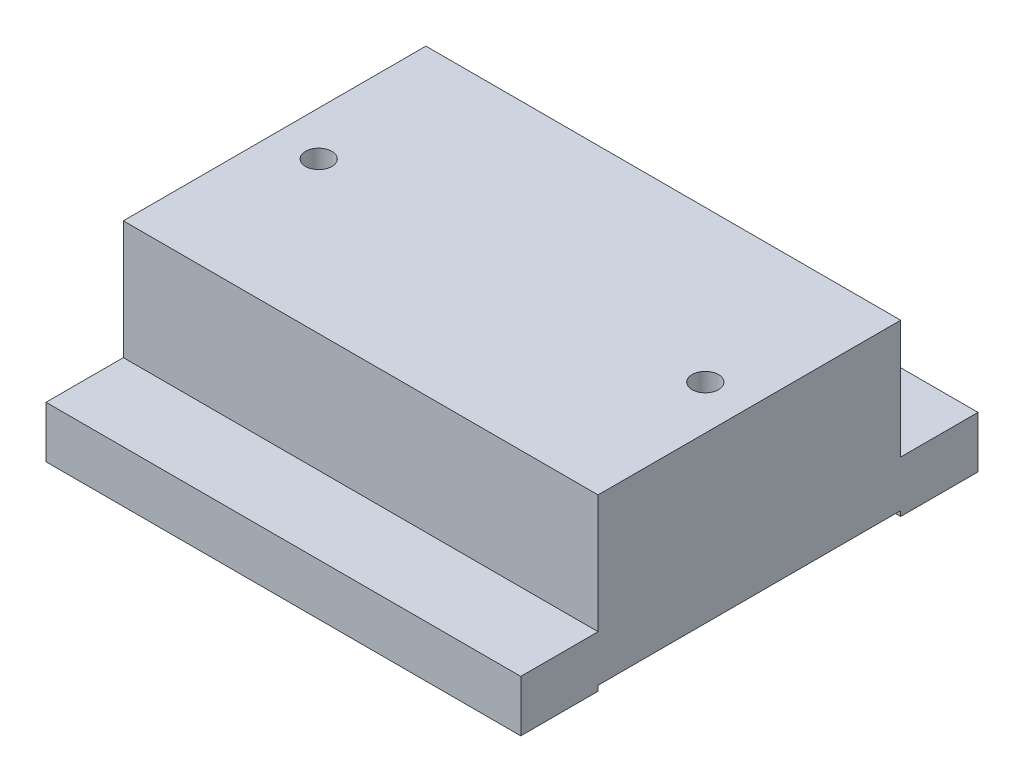
SolidWorks part; units mm, degrees
material "6061 Alloy"
ref_plane "Front" through (0, 0, 0) normal (0, 0, 1) x (1, 0, 0)
ref_plane "Top" through (0, 0, 0) normal (0, 1, 0) x (1, 0, 0)
ref_plane "Right" through (0, 0, 0) normal (1, 0, 0) x (0, 0, -1)
sketch "Sketch1" plane through (0, 0, 0) normal (0, 1, 0) x (1, 0, 0)
  line L1 (-46.05, 44.35) -> (46.05, 44.35)
  line L2 (-46.05, 44.35) -> (-46.05, -44.35)
  line L3 (-46.05, -44.35) -> (46.05, -44.35)
  line L4 (46.05, 44.35) -> (46.05, -44.35)
  line L5 (-46.05, 44.35) -> (46.05, -44.35) construction
  line L6 (-46.05, -44.35) -> (46.05, 44.35) construction
  point P0 (0, 0)
  dimension "D1" = 92.1
  dimension "D2" = 88.7
extrude "Boss-Extrude1" add sketch "Sketch1" along normal blind 10
sketch "Sketch2" plane through (0, 10, 0) normal (0, 1, 0) x (1, 0, 0)
  line L1 (-46.05, 29.35) -> (46.05, 29.35)
  line L2 (-46.05, 29.35) -> (-46.05, -29.35)
  line L3 (-46.05, -29.35) -> (46.05, -29.35)
  line L4 (46.05, 29.35) -> (46.05, -29.35)
  line L5 (-46.05, 29.35) -> (46.05, -29.35) construction
  line L6 (-46.05, -29.35) -> (46.05, 29.35) construction
  point P0 (0, 0)
  dimension "D1" = 58.7
  dimension "D2" = 92.1
extrude "Boss-Extrude2" add sketch "Sketch2" along normal blind 22.986
sketch "Sketch16" plane through (0, 0, 0) normal (0, -1, 0) x (1, 0, 0)
  line L0 (46.05, 44.35) -> (46.05, -44.35) construction
  line L1 (-46.05, 29.35) -> (46.05, 29.35)
  line L2 (-46.05, 29.35) -> (-46.05, -29.35)
  line L3 (-46.05, -29.35) -> (46.05, -29.35)
  line L4 (46.05, 29.35) -> (46.05, -29.35)
  line L5 (-46.05, 29.35) -> (46.05, -29.35) construction
  line L6 (-46.05, -29.35) -> (46.05, 29.35) construction
  line L7 (-46.05, 44.35) -> (46.05, 44.35) construction
  line L8 (46.05, -44.35) -> (-46.05, -44.35) construction
  point P0 (0, 0)
  dimension "D1" = 15
  dimension "D2" = 15
extrude "Cut-Extrude2" cut sketch "Sketch16" against normal blind 1
hole_wizard "1/4-20 Tapped Hole1" positions "Sketch27" profile "Sketch26" tap size "1/4-20" standard "Ansi Inch"
sketch "Sketch27" plane through (0, 32.986, 0) normal (0, 1, 0) x (-1, 0, 0)
  point P0 (37.5, 0)
  point P3 (-37.5, 0)
  dimension "D1" = 37.5
  dimension "D2" = 0
  dimension "D3" = 37.5
sketch "Sketch26" plane through (-37.5, 32.986, 0) normal (1, 0, 0) x (0, 0, 1)
  line L0 (0, 0) -> (0, 18.0438)
  line L1 (0, 18.0438) -> (2.5527, 16.51)
  line L2 (2.5527, 16.51) -> (2.5527, 0)
  line L5 (2.5527, 0) -> (0, 0)
  line L10 (0, 18.0438) -> (-2.5527, 16.51) construction
  line L11 (0, -6.35) -> (0, 107.95) construction
  dimension "Tap Drill Dia." = 5.1054
  dimension "Tap Drill Depth" = 16.51
  dimension "Drill Angle" = 118
